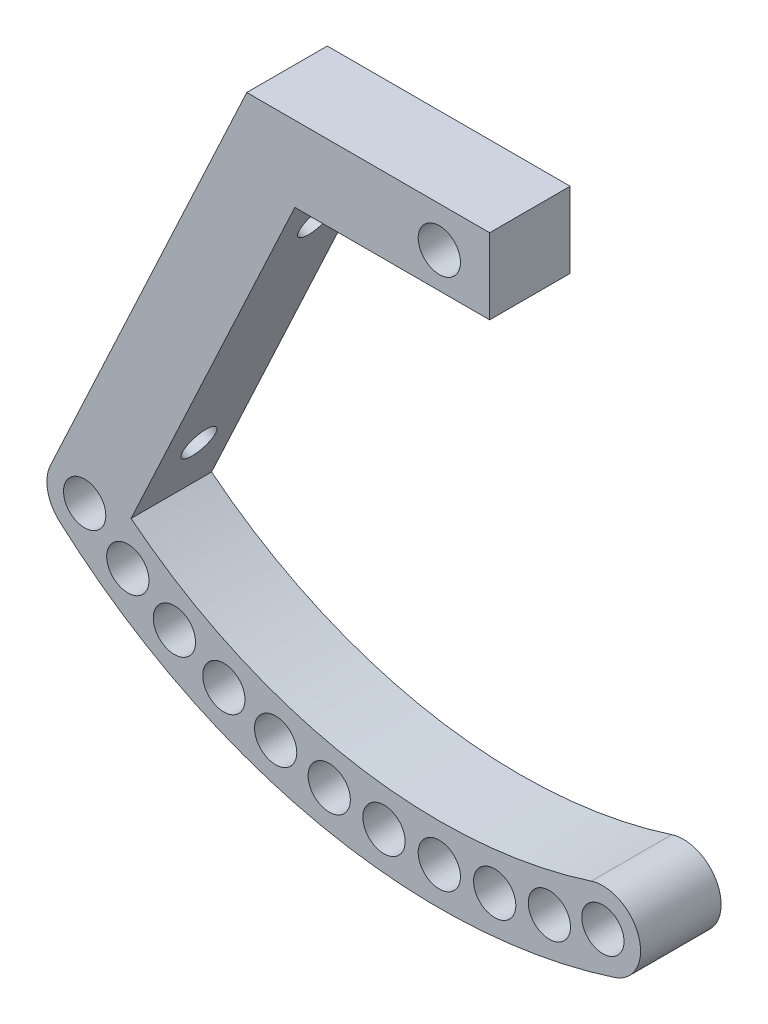
SolidWorks part; units mm, degrees
ref_plane "Front Plane" through (0, 0, 0) normal (0, 0, 1) x (1, 0, 0)
ref_plane "Top Plane" through (0, 0, 0) normal (0, 1, 0) x (1, 0, 0)
ref_plane "Right Plane" through (0, 0, 0) normal (1, 0, 0) x (0, 0, -1)
sketch "Sketch1" plane through (0, 0, 0) normal (0, 0, 1) x (1, 0, 0)
  line L0 (-26.3199, 30.1475) -> (-21.407, 27.6582) construction
  line L1 (-21.407, 27.6582) -> (-16.2619, 25.6935) construction
  line L2 (-16.2619, 25.6935) -> (-10.9403, 24.2748) construction
  line L3 (-10.9403, 24.2748) -> (-5.5, 23.4173) construction
  line L4 (-5.5, 23.4173) -> (0, 23.1304) construction
  line L5 (-35.2385, 36.5863) -> (-30.9471, 33.1343) construction
  line L6 (-30.9471, 33.1343) -> (-26.3199, 30.1475) construction
  line L7 (5, 72.5) -> (-19.132, 72.5)
  line L8 (5, 72.5) -> (5, 80)
  line L9 (-19.132, 72.5) -> (-19.132, 80)
  line L10 (5, 80) -> (-19.132, 80)
  line L12 (-19.132, 80) -> (-40.2876, 34.6316)
  line L13 (-19.132, 80) -> (-12.3347, 76.8304)
  line L14 (-40.2876, 34.6316) -> (-33.4903, 31.462)
  line L15 (-12.3347, 76.8304) -> (-33.4903, 31.462)
  line L16 (-15.7333, 78.4152) -> (-36.889, 33.0468) construction
  circle A0 centre (0, 76) radius 2.1
  circle A1 centre (16.2477, 25.6889) radius 2.1
  circle A2 centre (0, 23.1304) radius 2.1
  circle A3 centre (5.5, 23.4173) radius 2.1
  arc A4 (16.2477, 25.6889) -> (-35.2385, 36.5863) centre (0, 76) cw construction
  arc A5 (-37.7379, 33.7907) -> (17.4001, 22.1204) centre (0, 76) ccw
  arc A6 (-32.739, 39.3819) -> (15.0952, 29.2575) centre (0, 76) ccw
  arc A7 (-32.739, 39.3819) -> (-37.7379, 33.7907) centre (-35.2385, 36.5863) ccw
  arc A8 (17.4001, 22.1204) -> (15.0952, 29.2575) centre (16.2477, 25.6889) ccw
  circle A9 centre (-5.5, 23.4173) radius 2.1
  circle A10 centre (-10.9403, 24.2748) radius 2.1
  circle A11 centre (-16.2619, 25.6935) radius 2.1
  circle A12 centre (-21.407, 27.6582) radius 2.1
  circle A13 centre (-26.3199, 30.1475) radius 2.1
  circle A14 centre (-30.9471, 33.1343) radius 2.1
  circle A15 centre (-35.2385, 36.5863) radius 2.1
  circle A16 centre (10.933, 24.2732) radius 2.1
  point P12 (-10.9476, 24.2763)
  dimension "D1" = 7.5
  dimension "D2" = 5.5
  dimension "D3" = 7.5
  dimension "D5" = 5.5
  dimension "D6" = 4.2
  dimension "D7" = 4.2
  dimension "D8" = 4.2
  dimension "D9" = 4.2
  dimension "D4" = 115
  dimension "D10" = 5.5
  dimension "D11" = 5.5
extrude "Boss-Extrude1" add sketch "Sketch1" along normal blind 8 contours L13 L15 L7 L8 L10 A0 | L15 L13 L9 L7 | A7 A6 L15 L7 L9 L12 | A14 L15 A6 A7 A5 L14 A15 | A14 L15 L14 A5 A8 A6 A13 A12 A11 A10 A9 A1
ref_plane "Plane2" through (-46.5966, -82.6195, -9.525) normal (0, 0, -1) x (-0.7889, 0.6145, 0)
sketch "Sketch2" plane through (-46.3567, 21.6165, 0) normal (-0.9063, 0.4226, 0) x (0, 0, 1)
  line L0 (4, 64.4191) -> (4, 18.266) construction
  line L1 (8, 64.4191) -> (0, 64.4191) construction
  line L2 (8, 18.266) -> (0, 18.266) construction
  line L3 (4, 55.0426) -> (0, 64.4191) construction
  line L4 (4, 27.6426) -> (0, 18.266) construction
  circle A0 centre (4, 55.0426) radius 1.65
  circle A1 centre (4, 27.6426) radius 1.65
  dimension "D1" = 3.3
  dimension "D2" = 27.4
extrude "Cut-Extrude1" cut sketch "Sketch2" against normal up to next
